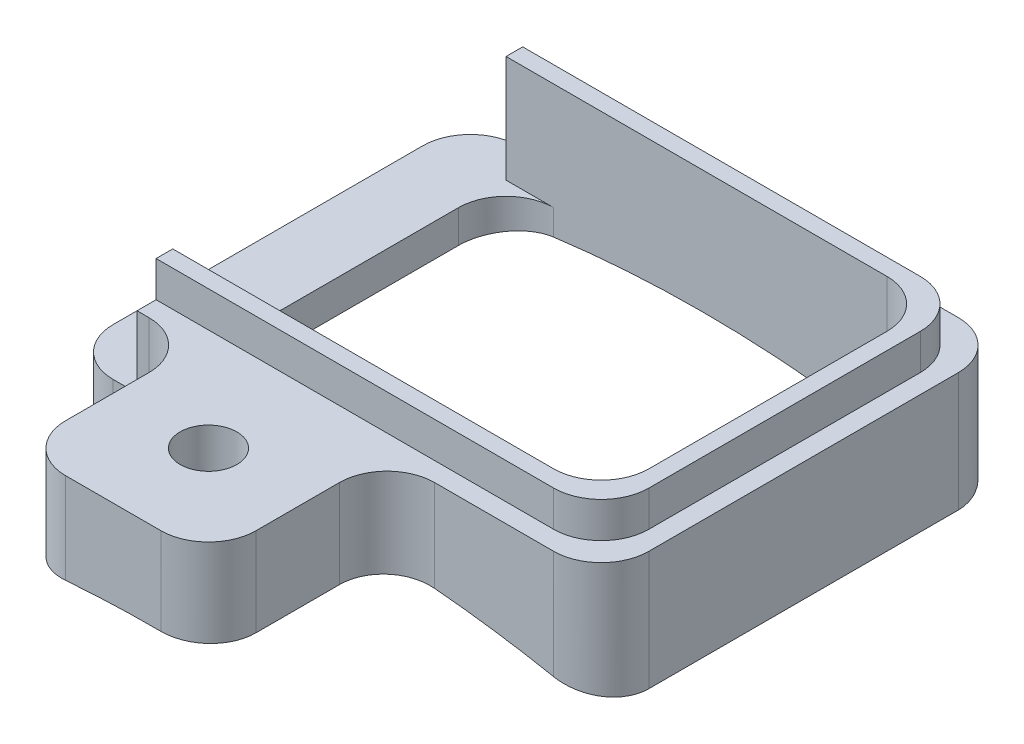
SolidWorks part; units mm, degrees
ref_plane "Front Plane" through (0, 0, 0) normal (0, 0, 1) x (1, 0, 0)
ref_plane "Top Plane" through (0, 0, 0) normal (0, 1, 0) x (1, 0, 0)
ref_plane "Right Plane" through (0, 0, 0) normal (1, 0, 0) x (0, 0, -1)
sketch "Sketch5" plane through (0, 0, 0) normal (0, 1, 0) x (1, 0, 0)
  line L1 (-5.625, -4.25) -> (5.625, -4.25)
  line L2 (-5.625, -4.25) -> (-5.625, 4.25)
  line L3 (-5.625, 4.25) -> (5.625, 4.25)
  line L4 (5.625, -4.25) -> (5.625, 4.25)
  line L5 (-5.625, -4.25) -> (5.625, 4.25) construction
  line L6 (-5.625, 4.25) -> (5.625, -4.25) construction
  point P0 (0, 0)
  dimension "D1" = 8.5
  dimension "D2" = 11.25
extrude "Extrude4" add sketch "Sketch5" along normal blind 2.5
sketch "Sketch19" plane through (0, 2.5, 0) normal (0, 1, 0) x (-1, 0, 0)
  line L0 (5.625, 4.25) -> (-5.625, 4.25) construction
  line L1 (5.625, -4.25) -> (4.125, -4.25)
  line L2 (5.625, -4.25) -> (5.625, 4.25)
  line L3 (5.625, 4.25) -> (4.125, 4.25)
  line L4 (4.125, -4.25) -> (4.125, 4.25)
  dimension "D1" = 1.5
extrude "Extrude12" cut sketch "Sketch19" against normal blind 1.5
sketch "Sketch21" plane through (0, 2.5, 0) normal (0, 1, 0) x (-1, 0, 0)
  line L0 (4.125, 4.25) -> (4.125, -4.25) construction
  line L1 (-4.875, -3.5) -> (4.125, -3.5)
  line L2 (-4.875, -3.5) -> (-4.875, 3.5)
  line L3 (-4.875, 3.5) -> (4.125, 3.5)
  line L4 (4.125, -3.5) -> (4.125, 3.5)
  line L5 (-5.625, -4.25) -> (4.125, -4.25) construction
  line L6 (-5.625, 4.25) -> (-5.625, -4.25) construction
  line L7 (4.125, 4.25) -> (-5.625, 4.25) construction
  dimension "D1" = 0.75
  dimension "D2" = 0.75
  dimension "D3" = 0.75
extrude "Extrude13" cut sketch "Sketch21" against normal through all
sketch "Sketch22" plane through (0, 0, 4.25) normal (0, 0, 1) x (1, 0, 0)
  line L0 (-4.125, 2.5) -> (5.625, 2.5) construction
  line L1 (-2.875, 2.5) -> (1.125, 2.5)
  line L2 (-2.875, 2.5) -> (-2.875, 0.1976)
  line L3 (-2.875, 0.1976) -> (1.125, 0.1976)
  line L4 (1.125, 2.5) -> (1.125, 0.1976)
  line L5 (5.625, 2.5) -> (5.625, 0) construction
  dimension "D1" = 4
  dimension "D2" = 4.5
extrude "Extrude14" add sketch "Sketch22" along normal blind 3.75
sketch "Sketch24" plane through (0, 2.5, 0) normal (0, 1, 0) x (1, 0, 0)
  line L0 (-4.125, 3.85) -> (-4.125, 3.5)
  line L1 (-4.125, 3.5) -> (4.875, 3.5)
  line L2 (4.875, 3.5) -> (4.875, -3.5)
  line L3 (4.875, -3.5) -> (-4.125, -3.5)
  line L4 (-4.125, -3.5) -> (-4.125, -3.85)
  line L9 (-4.125, -3.85) -> (5.225, -3.85)
  line L10 (5.225, -3.85) -> (5.225, 3.85)
  line L11 (5.225, 3.85) -> (-4.125, 3.85)
  line L12 (-4.125, -3.85) -> (5.225, -3.85)
  line L13 (5.225, -3.85) -> (5.225, 3.85)
  line L14 (5.225, 3.85) -> (-4.125, 3.85)
  dimension "D1" = 0.35
extrude "Extrude15" add sketch "Sketch24" along normal blind 0.75
sketch "Sketch33" plane through (0, 0, -4.25) normal (0, 0, -1) x (-1, 0, 0)
  line L0 (-5.625, 0) -> (5.625, 0) construction
  arc A0 (5.625, 0) -> (-5.625, 0) centre (0, -23.3315) ccw
extrude "Extrude18" cut sketch "Sketch33" against normal through all
hole_wizard "#0-80 Tapped Hole1" positions "3DSketch1" profile "Sketch26" tap size "#0-80" standard "Ansi Inch"
sketch3d "3DSketch1"
  line L2 (1.125, 2.5, 8) -> (-2.875, 2.5, 8) construction
  line L3 (1.125, 2.5, 8) -> (1.125, 2.5, 4.25) construction
  point P0 (-0.875, 2.5, 6)
  dimension "D1" = 2
  dimension "D2" = 2
sketch "Sketch26" plane through (-0.875, 2.5, 6) normal (1, 0, 0) x (0, 0, 1)
  line L0 (0, 0) -> (0, 79.3679)
  line L1 (0, 79.3679) -> (0.5956, 79.01)
  line L2 (0.5956, 79.01) -> (0.5956, 0)
  line L5 (0.5956, 0) -> (0, 0)
  line L10 (0, 79.3679) -> (-0.5956, 79.01) construction
  line L11 (0, -6.35) -> (0, 107.95) construction
  dimension "Tap Drill Dia." = 1.1913
  dimension "Tap Drill Depth" = 79.01
  dimension "Drill Angle" = 118
fillet "Fillet4" radius 1 14 edges at (5.625, 1.25, -4.25) (5.225, 2.875, -3.85) (5.625, 1.25, 4.25) (5.225, 2.875, 3.85) (4.875, 1.7091, 3.5) (4.875, 1.7091, -3.5) (-4.125, 0.6557, 3.5) (-4.125, 0.6557, -3.5) (-5.625, 0.5, -4.25) (-5.625, 0.5, 4.25) (-2.875, 1.4978, 8) (1.125, 1.5711, 8)
